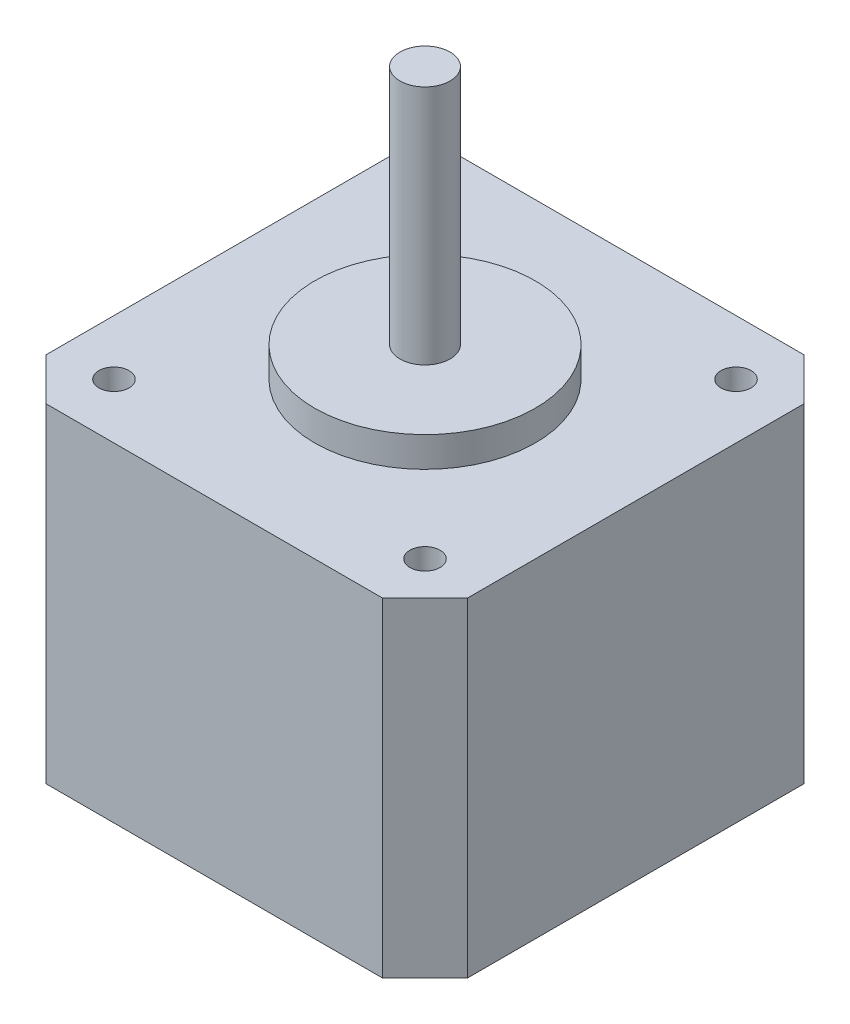
SolidWorks part; units mm, degrees
ref_plane "Front Plane" through (0, 0, 0) normal (0, 0, 1) x (1, 0, 0)
ref_plane "Top Plane" through (0, 0, 0) normal (0, 1, 0) x (1, 0, 0)
ref_plane "Right Plane" through (0, 0, 0) normal (1, 0, 0) x (0, 0, -1)
sketch "Sketch1" plane through (0, 0, 0) normal (0, 1, 0) x (1, 0, 0)
  line L0 (-19, 21) -> (-21, 19)
  line L1 (-19, 21) -> (16.76, 21)
  line L2 (-21, 19) -> (-21, -16.76)
  line L3 (-16.76, -21) -> (16.76, -21)
  line L4 (21, 16.76) -> (21, -16.76)
  line L5 (-21, 21) -> (21, -21) construction
  line L6 (-21, -21) -> (21, 21) construction
  line L7 (-21, -16.76) -> (-16.76, -21)
  line L8 (16.76, 21) -> (21, 16.76)
  line L9 (21, -16.76) -> (16.76, -21)
  line L10 (-1.12, 21) -> (-1.12, -21) construction
  line L11 (-21, 1.12) -> (21, 1.12) construction
  point P0 (0, 0)
  dimension "D1" = 42
extrude "Boss-Extrude1" add sketch "Sketch1" along normal blind 32.8
sketch "Sketch2" plane through (0, 32.8, 0) normal (0, 1, 0) x (1, 0, 0)
  line L0 (-18.88, -18.88) -> (18.88, 18.88) construction
  line L1 (-21, -16.76) -> (-16.76, -21) construction
  line L2 (21, 16.76) -> (16.76, 21) construction
  line L3 (-20, 20) -> (18.88, -18.88) construction
  line L4 (-19, 21) -> (-21, 19) construction
  line L5 (16.76, -21) -> (21, -16.76) construction
  line L6 (0, 21) -> (0, -21) construction
  line L7 (16.76, 21) -> (-19, 21) construction
  line L8 (-16.76, -21) -> (16.76, -21) construction
  line L9 (-21, 0) -> (21, 0) construction
  line L10 (-21, 19) -> (-21, -16.76) construction
  line L11 (21, -16.76) -> (21, 16.76) construction
  circle A0 centre (15.5, 15.5) radius 1.5
  circle A1 centre (15.5, -15.5) radius 1.5
  circle A2 centre (-15.5, -15.5) radius 1.5
  circle A3 centre (-15.5, 15.5) radius 1.5
  dimension "D1" = 3
  dimension "D2" = 31
extrude "Cut-Extrude1" cut sketch "Sketch2" against normal blind 10
sketch "Sketch3" plane through (0, 32.8, 0) normal (0, 1, 0) x (1, 0, 0)
  circle A0 centre (0, 0) radius 11
  dimension "D1" = 22
extrude "Boss-Extrude2" add sketch "Sketch3" along normal blind 3
sketch "Sketch4" plane through (0, 35.8, 0) normal (0, 1, 0) x (1, 0, 0)
  circle A0 centre (0, 0) radius 2.5
  dimension "D1" = 5
extrude "Boss-Extrude3" add sketch "Sketch4" along normal blind 24
